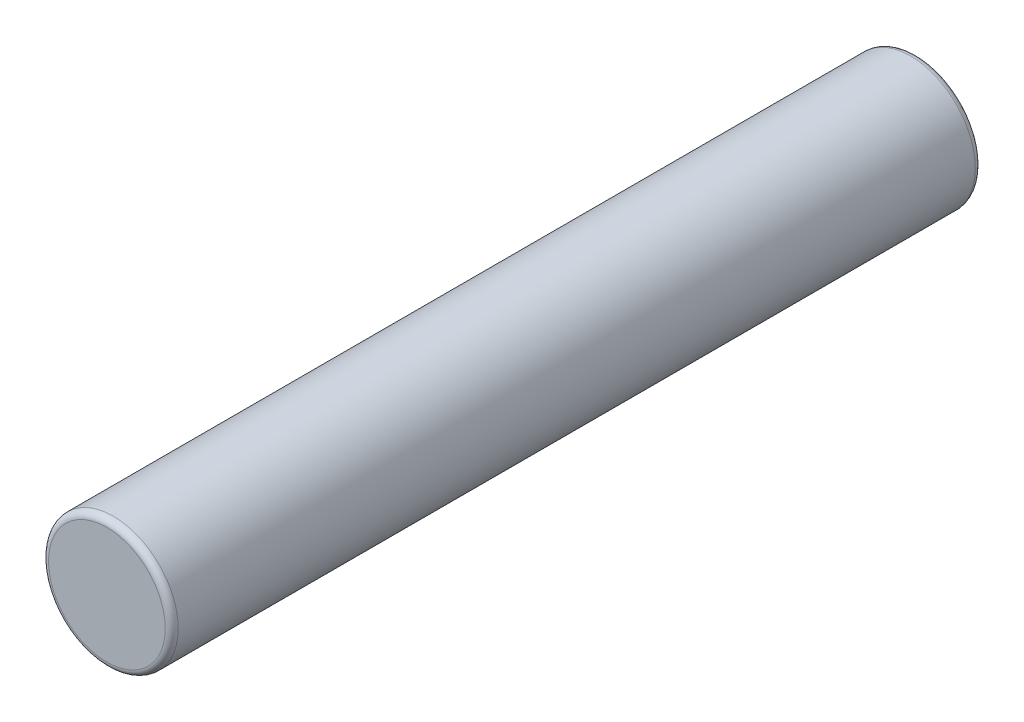
SolidWorks part; units mm, degrees
ref_plane "Ebene vorne" through (0, 0, 0) normal (0, 0, 1) x (1, 0, 0)
ref_plane "Ebene oben" through (0, 0, 0) normal (0, 1, 0) x (1, 0, 0)
ref_plane "Ebene rechts" through (0, 0, 0) normal (1, 0, 0) x (0, 0, -1)
sketch "Skizze1" plane through (0, 0, 0) normal (0, 0, 1) x (1, 0, 0)
  circle A0 centre (0, 0) radius 2
  dimension "D1" = 4
extrude "Aufsatz-Linear austragen1" add sketch "Skizze1" along normal blind 25
fillet "Verrundung2" radius 0.2 2 edges at (2, 0, 0) (2, 0, 25)
